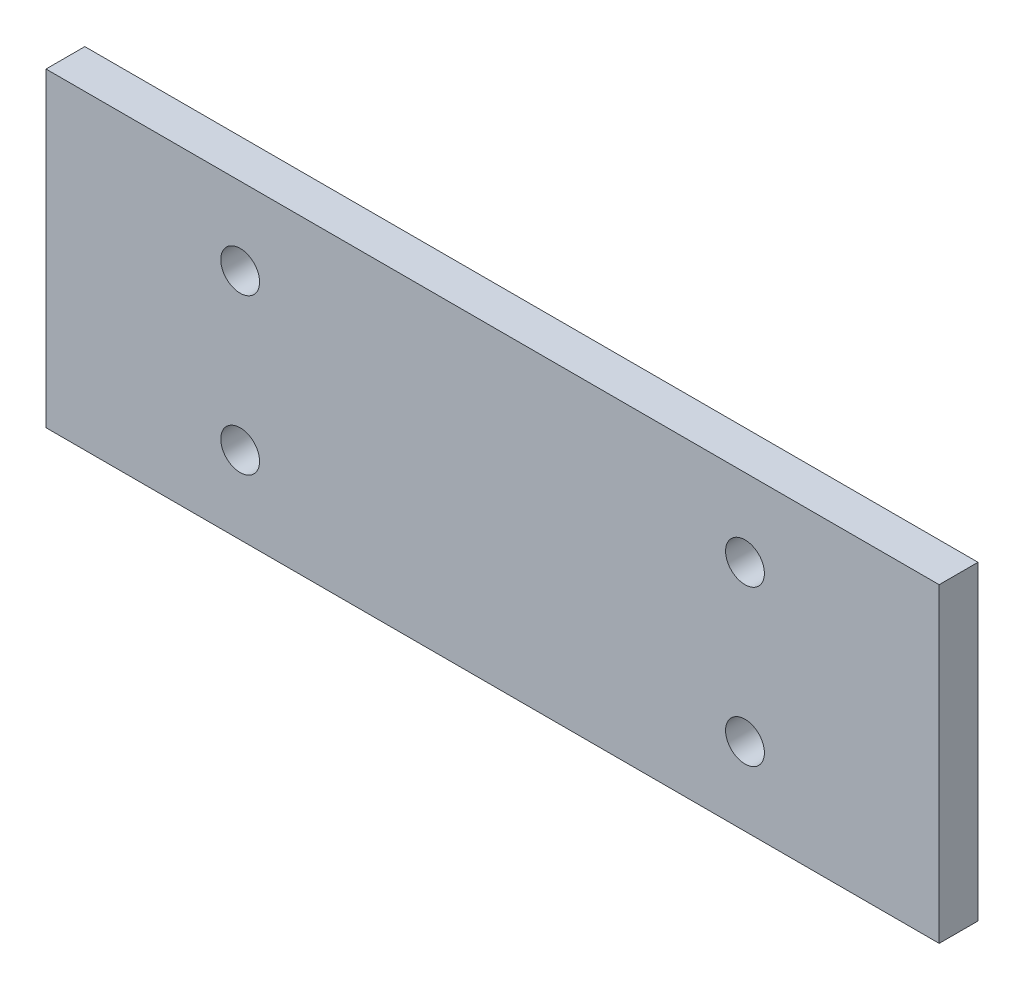
SolidWorks part; units mm, degrees
ref_plane "Front Plane" through (0, 0, 0) normal (0, 0, 1) x (1, 0, 0)
ref_plane "Top Plane" through (0, 0, 0) normal (0, 1, 0) x (1, 0, 0)
ref_plane "Right Plane" through (0, 0, 0) normal (1, 0, 0) x (0, 0, -1)
sketch "Sketch1" plane through (0, 0, 0) normal (0, 0, 1) x (1, 0, 0)
  line L0 (57.5, 71.5085) -> (57.5, -25.2788) construction
  line L1 (0, 0) -> (115, 0)
  line L2 (0, 0) -> (0, 40)
  line L3 (0, 40) -> (115, 40)
  line L4 (115, 0) -> (115, 40)
  line L5 (25, 71.5085) -> (25, -25.2788) construction
  line L6 (-33.2809, 30) -> (132.3942, 30) construction
  line L7 (-33.2809, 10) -> (132.3942, 10) construction
  line L8 (90, 71.5085) -> (90, -24.0733) construction
  circle A0 centre (25, 30) radius 2.5
  circle A1 centre (25, 10) radius 2.5
  circle A2 centre (90, 10) radius 2.5
  circle A3 centre (90, 30) radius 2.5
  dimension "D7" = 5
  dimension "D1" = 115
  dimension "D2" = 40
  dimension "D3" = 10
  dimension "D4" = 20
  dimension "D5" = 25
  dimension "D6" = 65
extrude "Boss-Extrude1" add sketch "Sketch1" along normal blind 5
